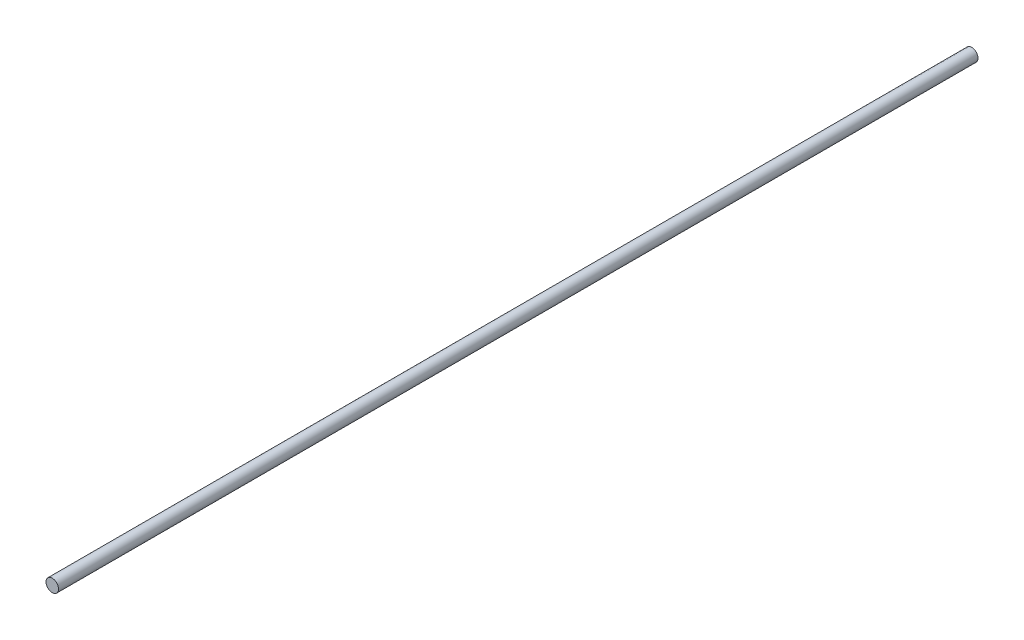
SolidWorks part; units mm, degrees
material "Malleable Cast Iron"
ref_plane "Front Plane" through (0, 0, 0) normal (0, 0, 1) x (1, 0, 0)
ref_plane "Top Plane" through (0, 0, 0) normal (0, 1, 0) x (1, 0, 0)
ref_plane "Right Plane" through (0, 0, 0) normal (1, 0, 0) x (0, 0, -1)
sketch "Sketch1" plane through (0, 0, 0) normal (0, 0, 1) x (1, 0, 0)
  circle A0 centre (0, 0) radius 5
  dimension "D1" = 10
extrude "Boss-Extrude1" add sketch "Sketch1" along normal blind 733
